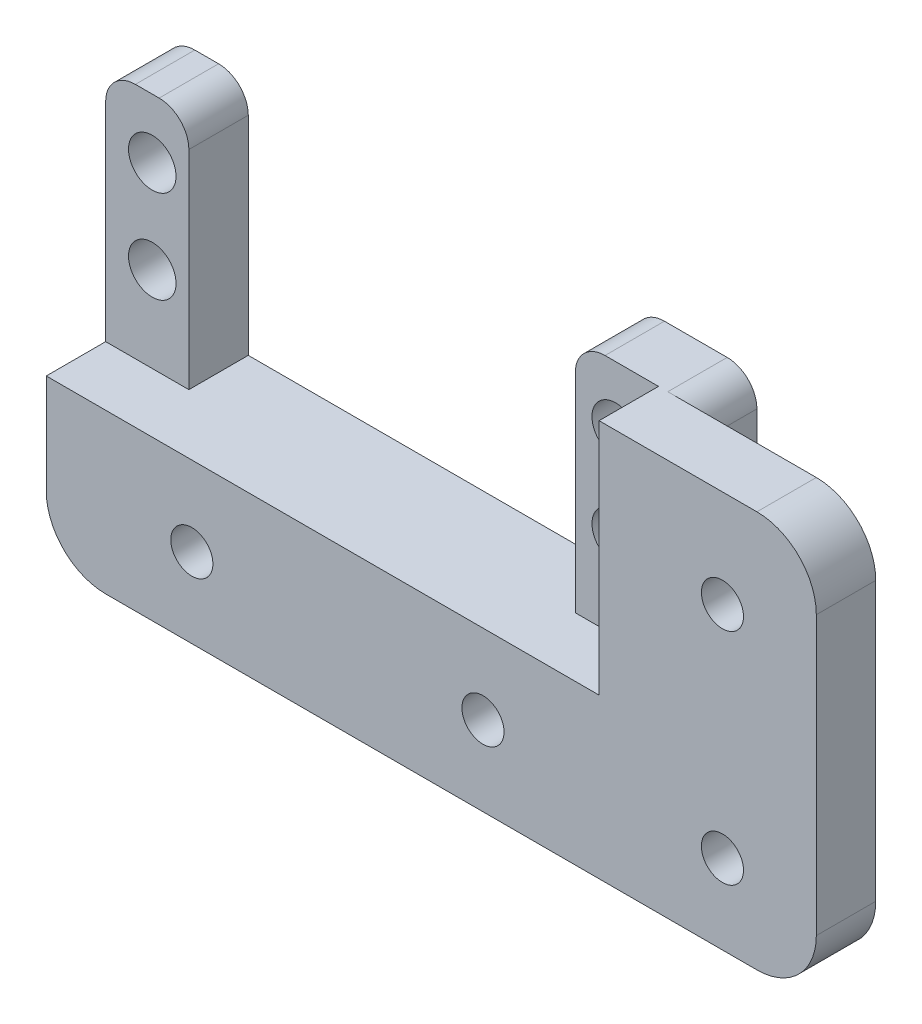
SolidWorks part; units mm, degrees
ref_plane "Front Plane" through (0, 0, 0) normal (0, 0, 1) x (1, 0, 0)
ref_plane "Top Plane" through (0, 0, 0) normal (0, 1, 0) x (1, 0, 0)
ref_plane "Right Plane" through (0, 0, 0) normal (1, 0, 0) x (0, 0, -1)
sketch "Sketch1" plane through (0, 0, 0) normal (0, 0, 1) x (1, 0, 0)
  line L8 (4000, 3.138) -> (4000, 8.5)
  line L10 (3773.94, 8.5) -> (3773.94, 3.138)
  line L11 (3773.94, 3.138) -> (4000, 3.138)
  line L12 (4000, -8.5) -> (4000, -3.138)
  line L13 (4000, -3.138) -> (3773.94, -3.138)
  line L14 (3773.94, -3.138) -> (3773.94, -8.5)
  line L15 (3781.2519, -8.5) -> (4000, -8.5)
  line L16 (3843.4819, 0) -> (3781.2519, 0)
  line L17 (3781.2519, 8.5) -> (3843.4819, 8.5)
  line L18 (3781.2519, 8.5) -> (3781.2519, -8.5)
  line L19 (3781.2519, -8.5) -> (3843.4819, -8.5)
  line L20 (3843.4819, 8.5) -> (3843.4819, -8.5)
  line L21 (3812.3669, 8.5) -> (3781.2519, -8.5)
  line L22 (3843.4819, -8.5) -> (3812.3669, 8.5)
  circle A0 centre (3827.9244, 0) radius 2.25
  circle A1 centre (3796.8094, 0) radius 2.25
  dimension "D1" = 62.23
extrude "Boss-Extrude1" add sketch "Sketch1" along normal blind 12.7 contours L15 L22 L13 L21 | A1 L21 L13 L22 A0 L16 | A0 L22 L13 L20 L16 | L22 L11 L20 L17 | A0 L16 L20 L11 L22 | A1 L16 A0 L22 L11 L21 | L11 L22 L21 | L21 L17 L18 L11 | A1 L21 L11 L18 L16 | A1 L16 L18 L13 L21 | L21 L13 L18 | L22 L20 L13
sketch "Sketch3" plane through (0, 8.5, 0) normal (0, 1, 0) x (1, 0, 0)
  line L0 (3831.4423, 0) -> (3831.4423, -6.35)
  line L1 (3781.2519, 0) -> (3843.4819, 0) construction
  line L2 (3831.4423, -6.35) -> (3840.3323, -6.35)
  line L3 (3840.3323, -6.35) -> (3840.3323, -12.7)
  line L4 (3781.2519, -12.7) -> (3843.4819, -12.7) construction
  line L5 (3840.3323, -12.7) -> (3843.4819, -12.7)
  line L6 (3843.4819, -12.7) -> (3843.4819, 0)
  line L7 (3843.4819, 0) -> (3831.4423, 0)
  dimension "D1" = 3.1496
  dimension "D2" = 8.89
  dimension "D3" = 6.35
extrude "Boss-Extrude2" add sketch "Sketch3" along normal blind 25.4
sketch "Sketch4" plane through (0, 8.5, 0) normal (0, 1, 0) x (1, 0, 0)
  line L0 (3781.2519, 0) -> (3790.1419, 0)
  line L1 (3781.2519, 0) -> (3831.4423, 0) construction
  line L2 (3790.1419, 0) -> (3790.1419, -6.35)
  line L3 (3790.1419, -6.35) -> (3781.2519, -6.35)
  line L4 (3781.2519, -12.7) -> (3781.2519, 0) construction
  line L5 (3781.2519, -6.35) -> (3781.2519, 0)
  line L6 (3831.4423, -6.35) -> (3840.3323, -6.35) construction
  dimension "D1" = 8.89
extrude "Boss-Extrude3" add sketch "Sketch4" along normal up to surface (25.4 mm away) up to face at (3838.4188, 33.9, 6.35)
sketch "Sketch5" plane through (0, 0, 6.35) normal (0, 0, 1) x (1, 0, 0)
  line L1 (3831.4423, 33.9) -> (3840.3323, 33.9) construction
  line L19 (3831.4423, 33.9) -> (3831.4423, 8.5) construction
  circle A0 centre (3835.7603, 27.55) radius 2.54
  circle A1 centre (3835.7603, 17.644) radius 2.54
  circle A2 centre (3786.2303, 17.644) radius 2.54
  circle A3 centre (3786.2303, 27.55) radius 2.54
  dimension "D1" = 4.318
  dimension "D3" = 5.08
  dimension "D2" = 6.35
  dimension "D4" = 9.906
  dimension "D5" = 49.53
extrude "Cut-Extrude1" cut sketch "Sketch5" against normal through all
sketch "Sketch6" plane through (0, 0, 0) normal (0, 0, -1) x (-1, 0, 0)
  line L0 (-3853.5149, 33.9) -> (-3853.5149, -8.5) construction
  line L1 (-3843.4819, -8.5) -> (-3863.5479, -8.5)
  line L2 (-3863.5479, -8.5) -> (-3863.5479, 33.9)
  line L3 (-3863.5479, 33.9) -> (-3843.4819, 33.9)
  line L4 (-3843.4819, 33.9) -> (-3843.4819, -8.5) construction
  line L5 (-3827.9244, 0) -> (-3853.5149, 0) construction
  circle A0 centre (-3853.5149, 23.4831) radius 2.25
  circle A1 centre (-3853.5149, 0) radius 2.25
  circle A2 centre (-3827.9244, 0) radius 2.25 construction
  line M10 (-3843.4819, 33.9) -> (-3843.4819, -8.5)
  dimension "D1" = 20.066
extrude "Boss-Extrude4" add sketch "Sketch6" against normal up to surface (12.7 mm away) contours L3 L2 L1 A1 A0 M10 up to face at (3821.6887, 11.3, 12.7)
sketch "Sketch7" plane through (0, 0, 0) normal (0, 0, -1) x (-1, 0, 0)
  circle A3 centre (-3827.9244, 0) radius 6.35
  circle A4 centre (-3796.8094, 0) radius 6.35
  circle M17 centre (-3827.9244, 0) radius 2.25
  circle M18 centre (-3796.8094, 0) radius 2.25
  dimension "D1" = 12.7
extrude "Cut-Extrude2" cut sketch "Sketch7" against normal offset from surface (6.35 mm away) 6.35 contours A3 M17 | A4 M18 up to face at (3828.3773, 11.3, 12.7)
sketch "Sketch8" plane through (0, 0, 0) normal (0, 0, -1) x (-1, 0, 0)
  line L0 (-3781.2519, -8.5) -> (-3863.5479, -8.5) construction
  line L1 (-3863.5479, 33.9) -> (-3844.4979, 33.9)
  line L2 (-3863.5479, 33.9) -> (-3863.5479, -8.5)
  line L3 (-3863.5479, -8.5) -> (-3844.4979, -8.5)
  line L4 (-3844.4979, 33.9) -> (-3844.4979, -8.5)
  dimension "D1" = 19.05
extrude "Cut-Extrude3" cut sketch "Sketch8" against normal blind 6.35
fillet "Fillet1" radius 6.35 4 edges at (3781.2519, -8.5, 6.35) (3863.5479, 33.9, 9.525) (3863.5479, -8.5, 9.525) (3844.4979, -8.5, 3.175)
fillet "Fillet2" radius 3.175 4 edges at (3844.4979, 33.9, 3.175) (3831.4423, 33.9, 3.175) (3781.2519, 33.9, 3.175) (3790.1419, 33.9, 3.175)
